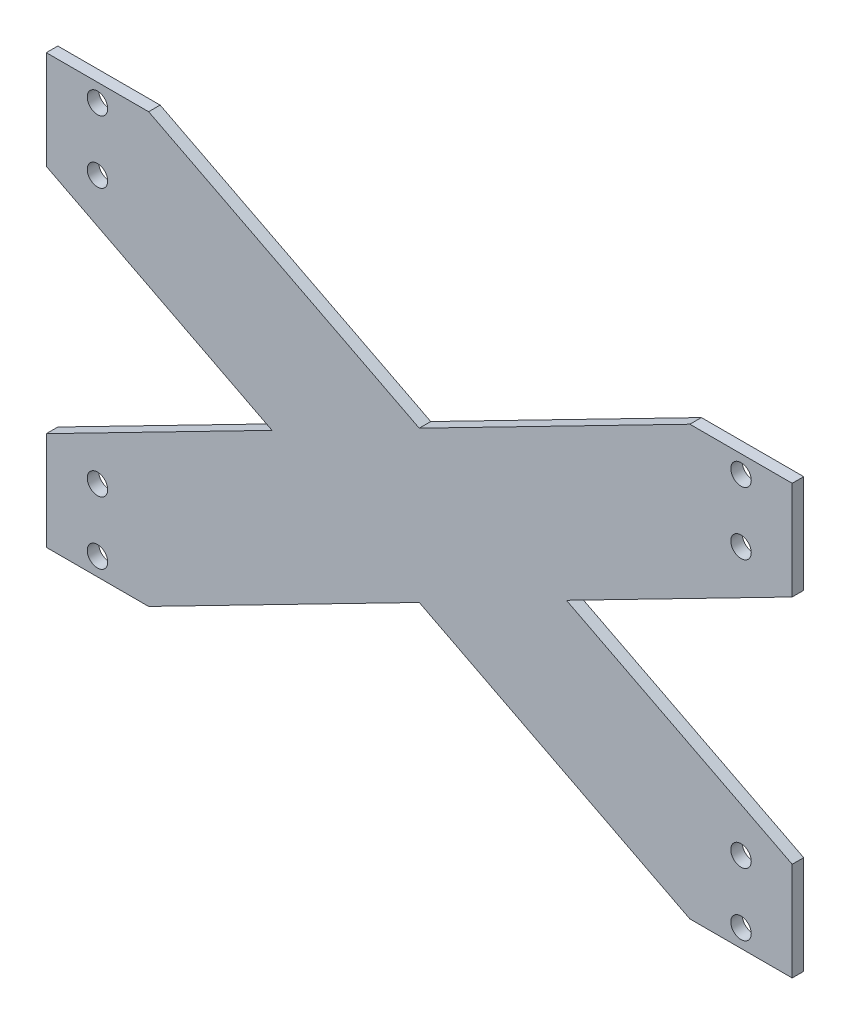
SolidWorks part; units mm, degrees
ref_plane "Front Plane" through (0, 0, 0) normal (0, 0, 1) x (1, 0, 0)
ref_plane "Top Plane" through (0, 0, 0) normal (0, 1, 0) x (1, 0, 0)
ref_plane "Right Plane" through (0, 0, 0) normal (1, 0, 0) x (0, 0, -1)
sketch "Sketch1" plane through (0, 0, 0) normal (0, 0, 1) x (1, 0, 0)
  line L0 (6.342, -18) -> (257.942, -147)
  line L1 (6.342, 20.5) -> (297.942, 20.5)
  line L2 (6.342, 20.5) -> (6.342, -147)
  line L3 (6.342, -147) -> (297.942, -147)
  line L4 (297.942, 20.5) -> (297.942, -147)
  line L5 (297.942, -108.5) -> (46.342, 20.5)
  line L6 (257.942, 20.5) -> (6.342, -108.5)
  line L7 (297.942, -18) -> (46.342, -147)
  circle A0 centre (26.342, 13.5) radius 4
  circle A1 centre (26.342, 13.5) radius 4 construction
  circle A2 centre (26.342, -11) radius 4
  circle A3 centre (26.342, -11) radius 4 construction
  circle A4 centre (26.342, -115.5) radius 4
  circle A5 centre (26.342, -140) radius 4
  circle A6 centre (26.342, -140) radius 4 construction
  circle A7 centre (26.342, -115.5) radius 4 construction
  circle A8 centre (277.942, 13.5) radius 4
  circle A9 centre (277.942, 13.5) radius 4 construction
  circle A10 centre (277.942, -11) radius 4
  circle A11 centre (277.942, -11) radius 4 construction
  circle A12 centre (277.942, -115.5) radius 4
  circle A13 centre (277.942, -115.5) radius 4 construction
  circle A14 centre (277.942, -140) radius 4
  circle A15 centre (277.942, -140) radius 4 construction
extrude "Boss-Extrude1" add sketch "Sketch1" along normal blind 4.5 contours L7 L0 L6 L2 L3 A5 A4 | L7 L5 L6 L0 | L6 L5 L1 L2 L0 A2 A0 | L7 L4 L1 L6 L5 A10 A8 | L5 L7 L0 L3 L4 A14 A12
